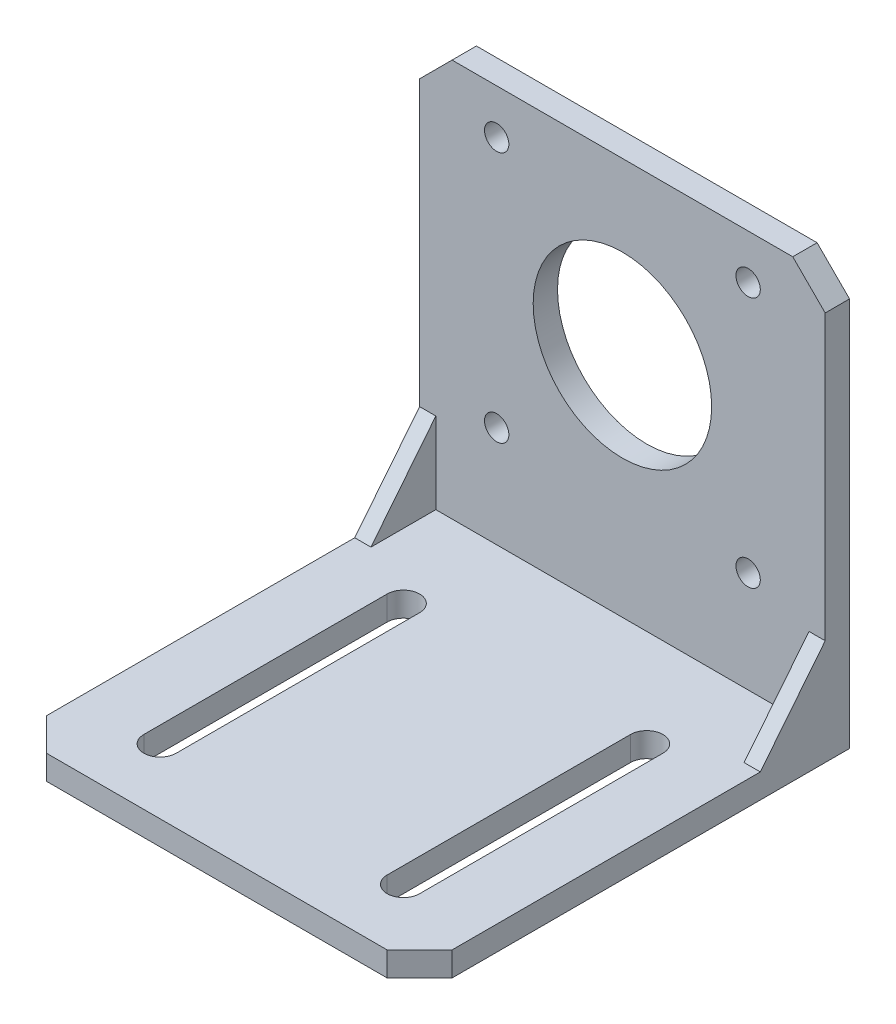
SolidWorks part; units mm, degrees
ref_plane "Front Plane" through (0, 0, 0) normal (0, 0, 1) x (1, 0, 0)
ref_plane "Top Plane" through (0, 0, 0) normal (0, 1, 0) x (1, 0, 0)
ref_plane "Right Plane" through (0, 0, 0) normal (1, 0, 0) x (0, 0, -1)
sketch "Sketch1" plane through (0, 0, 0) normal (0, 0, 1) x (1, 0, 0)
  line L0 (0, 0) -> (0, 26) construction
  line L1 (-25, 26) -> (25, 26)
  line L2 (-25, 26) -> (-25, -26)
  line L3 (-25, -26) -> (25, -26)
  line L4 (25, 26) -> (25, -26)
  line L5 (-25, 26) -> (25, -26) construction
  line L6 (-25, -26) -> (25, 26) construction
  line L8 (-15.5, -10.5) -> (15.5, -10.5) construction
  line L9 (-15.5, -10.5) -> (-15.5, 20.5) construction
  line L10 (-15.5, 20.5) -> (15.5, 20.5) construction
  line L11 (15.5, -10.5) -> (15.5, 20.5) construction
  line L12 (-15.5, -10.5) -> (15.5, 20.5) construction
  line L13 (-15.5, 20.5) -> (15.5, -10.5) construction
  circle A0 centre (0, 5) radius 11
  circle A1 centre (-15.5, 20.5) radius 1.5
  circle A2 centre (15.5, 20.5) radius 1.5
  circle A3 centre (15.5, -10.5) radius 1.5
  circle A4 centre (-15.5, -10.5) radius 1.5
  point P0 (0, 0)
  point P10 (0, 5)
  dimension "D3" = 22
  dimension "D6" = 3
  dimension "D1" = 50
  dimension "D2" = 52
  dimension "D4" = 21
  dimension "D5" = 31
extrude "Boss-Extrude1" add sketch "Sketch1" along normal blind 3
chamfer "Chamfer1" distance 4 angle 45 2 edges at (-25, 26, 1.5) (25, 26, 1.5)
sketch "Sketch2" plane through (0, 0, 3) normal (0, 0, 1) x (1, 0, 0)
  line L0 (25, -26) -> (25, 22) construction
  line L1 (-25, -26) -> (25, -26)
  line L2 (-25, -26) -> (-25, -23)
  line L3 (-25, -23) -> (25, -23)
  line L4 (25, -26) -> (25, -23)
  dimension "D1" = 3
extrude "Boss-Extrude2" add sketch "Sketch2" along normal offset from surface (50 mm away) 53 up to face at (0, 7.3333, 0)
sketch "Sketch3" plane through (25, 0, 0) normal (1, 0, 0) x (0, 0, -1)
  line L0 (-53, -23) -> (-3, -23) construction
  line L1 (-3, -23) -> (-3, 22) construction
  line L2 (-53, -23) -> (-3, -23)
  line L3 (-3, -23) -> (-3, 22)
  line L4 (-3, -13) -> (-11, -23)
  line M4 (-3, -23) -> (-53, -23)
  dimension "D1" = 8
  dimension "D2" = 10
extrude "Boss-Extrude3" add sketch "Sketch3" against normal blind 2 contours L3 L4 M4
sketch "Sketch4" plane through (-25, 0, 0) normal (-1, 0, 0) x (0, 0, 1)
  line L3 (3, -13) -> (3, -23)
  line L4 (3, -23) -> (11, -23)
  line L5 (11, -23) -> (3, -13)
  line L6 (3, -13) -> (3, -23)
  line L7 (3, -23) -> (11, -23)
  line L8 (11, -23) -> (3, -13)
  dimension "D1" = 0
extrude "Boss-Extrude4" add sketch "Sketch4" against normal blind 2
chamfer "Chamfer2" distance 4 angle 45 2 edges at (25, -24.5, 53) (-25, -24.5, 53)
sketch "Sketch5" plane through (0, -23, 0) normal (0, 1, 0) x (1, 0, 0)
  line L0 (0, 0) -> (0, -53) construction
  line L1 (21, 0) -> (-21, 0) construction
  line L2 (21, -53) -> (-21, -53) construction
  line L3 (-15, -15) -> (-15, -45) construction
  line L4 (-13, -15) -> (-13, -45)
  line L5 (-17, -15) -> (-17, -45)
  line L6 (15, -15) -> (15, -45) construction
  line L7 (13, -15) -> (13, -45)
  line L8 (17, -15) -> (17, -45)
  arc A0 (-13, -15) -> (-17, -15) centre (-15, -15) ccw
  arc A1 (-17, -45) -> (-13, -45) centre (-15, -45) ccw
  arc A2 (13, -15) -> (17, -15) centre (15, -15) cw
  arc A3 (17, -45) -> (13, -45) centre (15, -45) cw
  point P8 (-15, -30)
  point P15 (15, -30)
  dimension "D2" = 34
  dimension "D1" = 4
  dimension "D3" = 15
  dimension "D4" = 8
extrude "Cut-Extrude1" cut sketch "Sketch5" against normal through all
